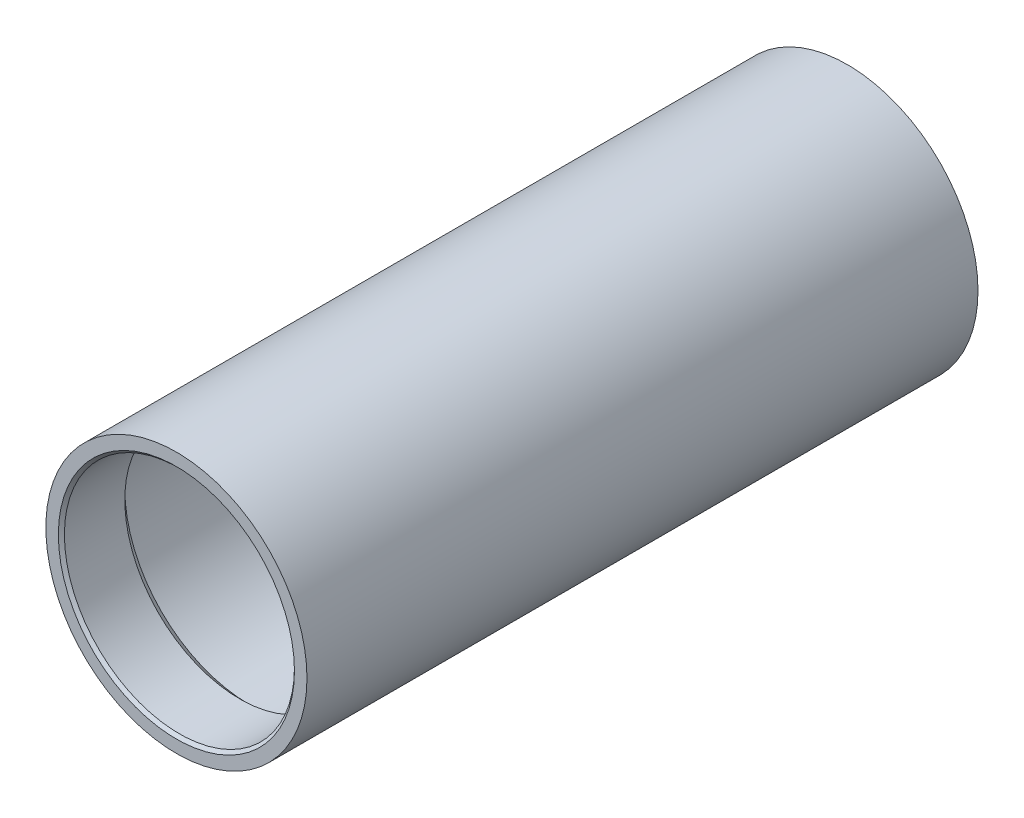
SolidWorks part; units mm, degrees
material "6061-T6 (SS)"
ref_plane "Front" through (0, 0, 0) normal (0, 0, 1) x (1, 0, 0)
ref_plane "Top" through (0, 0, 0) normal (0, 1, 0) x (1, 0, 0)
ref_plane "Right" through (0, 0, 0) normal (1, 0, 0) x (0, 0, -1)
sketch "Sketch1" plane through (0, 0, 0) normal (1, 0, 0) x (0, 0, -1)
  line L0 (0, 43.2435) -> (222.25, 43.2435)
  line L1 (0, 0) -> (222.25, 0) construction
  line L2 (0, 43.2435) -> (0, 38.1)
  line L3 (0, 38.1) -> (21, 38.1)
  line L4 (21, 38.1) -> (24.2385, 41.3385)
  line L5 (24.2385, 41.3385) -> (106.7865, 41.3385)
  line L6 (106.7865, 41.3385) -> (108.625, 39.5)
  line L7 (108.625, 39.5) -> (113.625, 39.5)
  line L8 (113.625, 39.5) -> (115.4635, 41.3385)
  line L9 (115.4635, 41.3385) -> (198.0115, 41.3385)
  line L10 (198.0115, 41.3385) -> (201.25, 38.1)
  line L11 (201.25, 38.1) -> (222.25, 38.1)
  line L12 (222.25, 38.1) -> (222.25, 43.2435)
  point P4 (111.125, 39.5)
  point P16 (111.125, 43.2435)
  dimension "D1" = 222.25
  dimension "D2" = 38.1
  dimension "D3" = 43.2435
  dimension "D4" = 21
  dimension "D5" = 135
  dimension "D6" = 38.1
  dimension "D7" = 1.905
  dimension "D8" = 1.905
  dimension "D9" = 21
  dimension "D10" = 5
  dimension "D11" = 39.5
revolve "Revolve1" add sketch "Sketch1" angle 360 about L1
chamfer "Chamfer1" distance 1 angle 45 2 edges at (38.1, 0, 0) (38.1, 0, -222.25)
